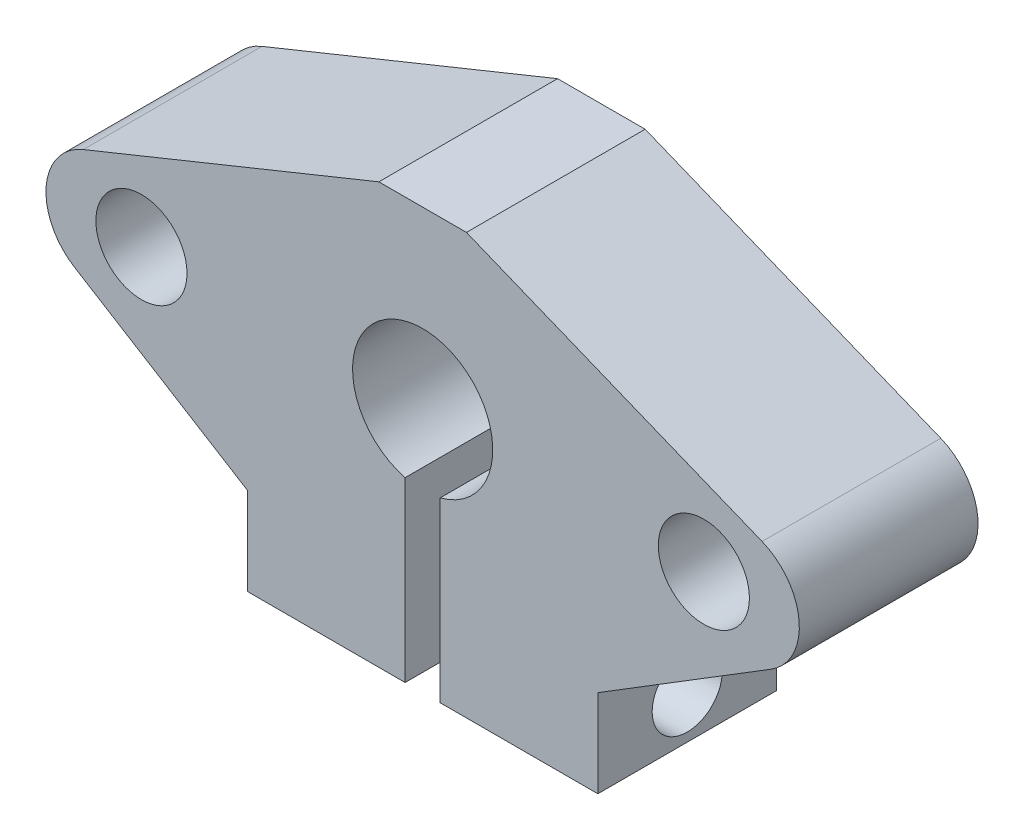
SolidWorks part; units mm, degrees
material "6063-O"
ref_plane "Alzado" through (0, 0, 0) normal (0, 0, 1) x (1, 0, 0)
ref_plane "Planta" through (0, 0, 0) normal (0, 1, 0) x (1, 0, 0)
ref_plane "Vista lateral" through (0, 0, 0) normal (1, 0, 0) x (0, 0, -1)
sketch "Croquis1" plane through (0, 0, 0) normal (0, 0, 1) x (1, 0, 0)
  line L0 (-10, 0) -> (10, 0)
  line L1 (10, 0) -> (10, 5)
  line L2 (10, 5) -> (19.8813, 11.0987)
  line L3 (19.3716, 17.1596) -> (2.5, 24)
  line L4 (2.5, 24) -> (-2.5, 24)
  line L5 (-2.5, 24) -> (-19.3716, 17.1596)
  line L6 (-19.8813, 11.0987) -> (-10, 5)
  line L7 (-10, 5) -> (-10, 0)
  line L8 (-16.05, 14) -> (16.05, 14) construction
  line L9 (-18.0906, 14) -> (-18.0906, 11.1865) construction
  line L10 (-18.0906, 11.1865) -> (18.0906, 11.1865) construction
  line L11 (18.0906, 11.1865) -> (18.0906, 14) construction
  circle A0 centre (0, 14) radius 4
  circle A1 centre (16.05, 14) radius 2.6
  circle A2 centre (-16.05, 14) radius 2.6
  arc A3 (19.8813, 11.0987) -> (19.3716, 17.1596) centre (18.0906, 14) ccw
  arc A4 (-19.3716, 17.1596) -> (-19.8813, 11.0987) centre (-18.0906, 14) ccw
  point P3 (0, 0)
  point P19 (0, 14)
  point P21 (0, 11.1865)
  point P28 (0, 24)
  dimension "D2" = 8
  dimension "D3" = 5.2
  dimension "D5" = 43
  dimension "D11" = 3.4094
  dimension "D1" = 10
  dimension "D4" = 37.3
  dimension "D6" = 20
  dimension "D7" = 5
  dimension "D8" = 5
  dimension "D9" = 5
  dimension "D10" = 24
extrude "Saliente-Extruir2" add sketch "Croquis1" along normal blind 10.2
sketch "Croquis3" plane through (0, 0, 10.2) normal (0, 0, 1) x (1, 0, 0)
  line L0 (-1, 0) -> (-1, 10.127)
  line L1 (-10, 0) -> (10, 0) construction
  line L2 (-1, 0) -> (1, 0)
  line L3 (1, 0) -> (1, 10.127)
  circle A0 centre (0, 14) radius 4 construction
  arc A1 (-1, 10.127) -> (1, 10.127) centre (0, 14) ccw
  point P9 (0, 0)
  dimension "D1" = 2
extrude "Cortar-Extruir3" cut sketch "Croquis3" against normal through all
sketch "Croquis4" plane through (10, 0, 0) normal (1, 0, 0) x (0, 0, -1)
  line L0 (0, 0) -> (0, 5) construction
  line L1 (-10.2, 0) -> (0, 0) construction
  circle A0 centre (-5.1, 2.5) radius 2
  point P5 (0, 2.5)
  point P9 (-5.1, 0)
  dimension "D1" = 4
extrude "Cortar-Extruir4" cut sketch "Croquis4" against normal through all and the other way through all
